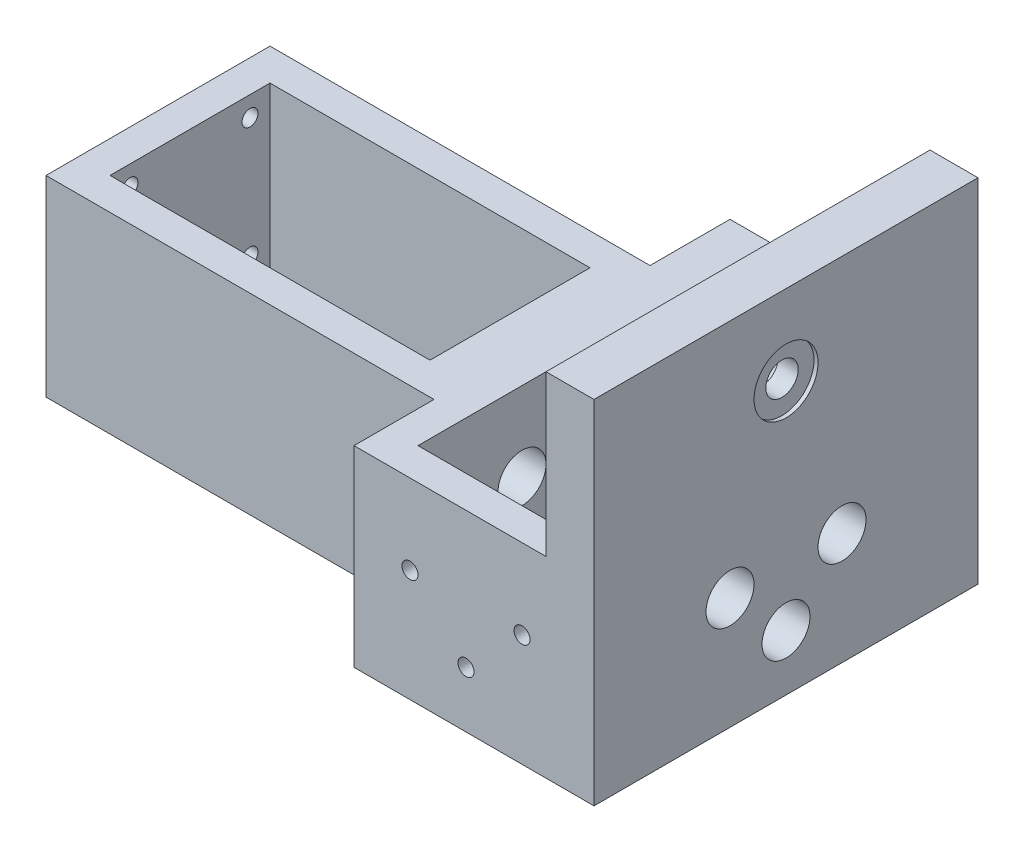
SolidWorks part; units mm, degrees
ref_plane "Front Plane" through (0, 0, 0) normal (0, 0, 1) x (1, 0, 0)
ref_plane "Top Plane" through (0, 0, 0) normal (0, 1, 0) x (1, 0, 0)
ref_plane "Right Plane" through (0, 0, 0) normal (1, 0, 0) x (0, 0, -1)
sketch "Sketch1" plane through (0, 0, 0) normal (0, 1, 0) x (1, 0, 0)
  line L0 (0, 0) -> (0, 20) construction
  line L1 (0, 20) -> (40, 20) construction
  line L2 (40, 20) -> (40, 0) construction
  line L3 (40, 0) -> (0, 0) construction
  line L4 (0, 20) -> (-5, 20) construction
  line L5 (40, 20) -> (45, 20) construction
  line L6 (-5, 20) -> (-5, 0) construction
  line L7 (-5, 0) -> (0, 0) construction
  line L8 (40, 20) -> (48.5, 20) construction
  line L9 (45, 0) -> (40, 0) construction
  line L10 (45, 20) -> (45, 0) construction
  line L11 (40, 0) -> (48.5, 0) construction
  line L12 (48.5, 0) -> (48.5, 20) construction
  line L13 (48.5, 10) -> (48.5, 30) construction
  line L14 (48.5, 10) -> (48.5, -10) construction
  line L15 (48.5, -10) -> (68.5, -10) construction
  line L16 (48.5, 30) -> (68.5, 30) construction
  line L17 (68.5, 30) -> (68.5, -10) construction
  line L18 (48.5, 20) -> (43.5, 20) construction
  line L19 (43.5, 20) -> (43.5, 30) construction
  line L20 (43.5, 30) -> (43.5, 35) construction
  line L21 (43.5, 35) -> (68.5, 35) construction
  line L22 (68.5, 35) -> (73.5, 35) construction
  line L23 (73.5, 35) -> (73.5, -10) construction
  line L24 (73.5, -10) -> (73.5, -15) construction
  line L25 (73.5, -15) -> (43.5, -15) construction
  line L26 (43.5, -15) -> (43.5, 20) construction
  line L27 (-5, 20) -> (43.5, 20)
  line L28 (43.5, 20) -> (43.5, 35)
  line L29 (43.5, 35) -> (73.5, 35)
  line L30 (73.5, 35) -> (73.5, -15)
  line L31 (73.5, -15) -> (43.5, -15)
  line L32 (43.5, -15) -> (43.5, 0)
  line L33 (43.5, 0) -> (-5, 0)
  line L34 (-5, 0) -> (-5, 20)
  line L35 (-5, 10) -> (73.5, 10) construction
extrude "Boss-Extrude1" add sketch "Sketch1" along normal blind 5
sketch "Sketch2" plane through (0, 5, 0) normal (0, 1, 0) x (1, 0, 0)
  line L0 (-5, 20) -> (0, 20) construction
  line L1 (43.5, 20) -> (-5, 20) construction
  line L2 (0, 20) -> (0, 0) construction
  line L3 (0, 0) -> (-5, 0) construction
  line L4 (-5, 0) -> (-5, 20) construction
  line L5 (0, 20) -> (40, 20) construction
  line L6 (40, 20) -> (40, 0) construction
  line L7 (-5, 0) -> (43.5, 0) construction
  line L8 (73.5, 35) -> (68.5, 35) construction
  line L9 (68.5, 35) -> (68.5, -15) construction
  line L10 (43.5, -15) -> (73.5, -15) construction
  line L11 (43.5, 35) -> (48.5, 35) construction
  line L12 (48.5, 35) -> (48.5, -15) construction
  line L13 (43.5, 35) -> (43.5, 30) construction
  line L14 (43.5, 30) -> (73.5, 30) construction
  line L15 (73.5, -15) -> (73.5, 35) construction
  line L16 (73.5, -15) -> (73.5, -10) construction
  line L17 (73.5, -10) -> (43.5, -10) construction
  line L18 (43.5, 0) -> (43.5, -15) construction
  line L19 (40, 20) -> (43.5, 20)
  line L20 (-5, 20) -> (0, 20)
  line L21 (-5, 20) -> (-5, 0)
  line L22 (-5, 0) -> (0, 0)
  line L23 (0, 20) -> (0, 0)
  line L24 (48.5, 30) -> (68.5, 30)
  line L25 (48.5, 30) -> (48.5, -10)
  line L26 (48.5, -10) -> (68.5, -10)
  line L27 (68.5, 30) -> (68.5, -10)
  line L28 (43.5, 20) -> (43.5, 35)
  line L29 (43.5, 35) -> (73.5, 35)
  line L30 (73.5, 35) -> (73.5, -15)
  line L31 (73.5, -15) -> (43.5, -15)
  line L32 (43.5, -15) -> (43.5, 0)
  line L33 (43.5, 0) -> (40, 0)
  line L34 (40, 0) -> (40, 20)
extrude "Boss-Extrude2" add sketch "Sketch2" along normal blind 20
sketch "Sketch3" plane through (0, 0, 0) normal (0, 0, 1) x (1, 0, 0)
  line L0 (43.5, 25) -> (-5, 25)
  line L1 (-5, 25) -> (-5, 0)
  line L2 (-5, 0) -> (43.5, 0)
  line L3 (43.5, 0) -> (43.5, 25)
extrude "Boss-Extrude3" add sketch "Sketch3" along normal blind 4
sketch "Sketch4" plane through (0, 0, -20) normal (0, 0, -1) x (-1, 0, 0)
  line L0 (-43.5, 25) -> (5, 25)
  line L1 (5, 25) -> (5, 0)
  line L2 (5, 0) -> (-43.5, 0)
  line L3 (-43.5, 0) -> (-43.5, 25)
extrude "Boss-Extrude4" add sketch "Sketch4" along normal blind 4
sketch "Sketch6" plane through (0, 0, 0) normal (0, -1, 0) x (1, 0, 0)
  line L0 (73.5, 15) -> (72.5, 15) construction
  line L1 (72.5, 15) -> (72.5, -35) construction
  line L2 (73.5, -35) -> (43.5, -35) construction
  line L3 (73.5, -35) -> (73.5, -34) construction
  line L4 (73.5, -34) -> (43.5, -34) construction
  line L5 (43.5, -35) -> (43.5, -24) construction
  line L6 (43.5, 15) -> (44.5, 15) construction
  line L7 (43.5, 15) -> (73.5, 15) construction
  line L8 (44.5, 15) -> (44.5, 14) construction
  line L9 (72.5, -34) -> (72.5, 14)
  line L10 (72.5, 14) -> (44.5, 14)
  line L11 (43.5, 4) -> (44.5, 4) construction
  line L12 (43.5, 4) -> (44.5, 4)
  line L13 (44.5, 4) -> (44.5, 14)
  line L14 (43.5, 4) -> (42.1751, 8.832)
  line L15 (42.1751, 8.832) -> (-3.5645, 8.832)
  line L16 (-5, 4) -> (-4, 4) construction
  line L17 (-5, 4) -> (43.5, 4) construction
  line L18 (-4, 4) -> (-4, 8.832) construction
  line L19 (-3.5645, 8.832) -> (-4, 4)
  line L20 (-4, 4) -> (-4, -32.6512)
  line L21 (-4, -32.6512) -> (43.5, -34)
  line L22 (43.5, -34) -> (72.5, -34)
  line L24 (-127.2585, 77.6513) -> (166.7327, 77.6513)
  line L25 (-127.2585, 77.6513) -> (-127.2585, -88.9607)
  line L26 (-127.2585, -88.9607) -> (166.7327, -88.9607)
  line L27 (166.7327, 77.6513) -> (166.7327, -88.9607)
extrude "Cut-Extrude1" cut sketch "Sketch6" against normal blind 218
sketch "Sketch7" plane through (0, 25, 0) normal (0, 1, 0) x (1, 0, 0)
  line L0 (44.5, -14) -> (72.5, -14) construction
  line L1 (72.5, 34) -> (68.5, 34)
  line L2 (72.5, 34) -> (72.5, -14)
  line L3 (72.5, -14) -> (68.5, -14)
  line L4 (68.5, 34) -> (68.5, -14)
extrude "Boss-Extrude5" add sketch "Sketch7" along normal blind 20
sketch "Sketch8" plane through (-4, 0, 0) normal (-1, 0, 0) x (0, 0, 1)
  line L0 (-10, 0) -> (-10, 25) construction
  line L1 (4, 0) -> (-24, 0) construction
  line L2 (-24, 25) -> (4, 25) construction
  line L3 (-10, 25) -> (-10, 0) construction
  line L4 (-10, 0) -> (-10, 5) construction
  line L5 (-10, 5) -> (4, 5) construction
  line L6 (4, 25) -> (4, 0) construction
  line L7 (4, 5) -> (4, 25) construction
  line L8 (4, 25) -> (4, 0) construction
  line L9 (-34, 25) -> (-34, 0) construction
  line L10 (14, 0) -> (-34, 0)
  line L11 (14, 0) -> (14, 1)
  line L12 (14, 1) -> (-34, 1)
  line L13 (-34, 0) -> (-34, 1)
extrude "Cut-Extrude2" cut sketch "Sketch8" against normal blind 87
sketch "Sketch9" plane through (-4, 0, 0) normal (-1, 0, 0) x (0, 0, 1)
  line L0 (-10, 25) -> (-10, 1) construction
  line L1 (-24, 25) -> (4, 25) construction
  line L2 (4, 1) -> (-24, 1) construction
  line L3 (-10, 1) -> (-10, 5) construction
  line L4 (-10, 5) -> (4, 5) construction
  line L5 (4, 5) -> (-24, 5) construction
  line L6 (-24, 25) -> (-24, 1) construction
  line L7 (-24, 5) -> (-20, 5) construction
  line L8 (-20, 5) -> (-20, 25) construction
  line L9 (-20, 25) -> (4, 25) construction
  line L10 (4, 25) -> (4, 5) construction
  line L11 (4, 5) -> (0, 5) construction
  line L12 (0, 5) -> (0, 25) construction
  line L13 (-10, 5) -> (-2.5, 5) construction
  line L14 (-2.5, 5) -> (-2.5, 25) construction
  line L15 (-2.5, 25) -> (-17.5, 25) construction
  line L16 (-17.5, 25) -> (-17.5, 5) construction
  line L17 (-2.5, 15) -> (-2.5, 22.5) construction
  line L18 (-2.5, 22.5) -> (-17.5, 22.5) construction
  line L19 (-2.5, 15) -> (-17.5, 15) construction
  circle A0 centre (-2.5, 22.5) radius 1
  circle A1 centre (-17.5, 22.5) radius 1
  circle A2 centre (-17.5, 7.5) radius 1
  circle A3 centre (-2.5, 7.5) radius 1
extrude "Cut-Extrude3" cut sketch "Sketch9" against normal blind 10
sketch "Sketch10" plane through (40, 0, 0) normal (-1, 0, 0) x (0, 0, 1)
  line L0 (-20, 25) -> (0, 25) construction
  line L1 (-20, 25) -> (0, 25) construction
  line L2 (-30, 25) -> (10, 25) construction
  line L3 (0, 25) -> (-10, 25) construction
  line L4 (-10, 25) -> (-10, 1) construction
  line L5 (-34, 1) -> (14, 1) construction
  line L6 (-10, 1) -> (-10, 5) construction
  line L7 (-10, 5) -> (-10, 8) construction
  line L8 (-10, 8) -> (-20, 8) construction
  line L9 (-20, 8) -> (0, 8) construction
  line L10 (0, 25) -> (0, 5) construction
  line L11 (-30, 5) -> (10, 5) construction
  line L12 (0, 5) -> (-20, 5) construction
  line L13 (-20, 5) -> (-20, 25) construction
  line L14 (-20, 25) -> (-17, 25) construction
  line L15 (-17, 25) -> (-17, 5) construction
  line L16 (-3, 25) -> (-3, 5) construction
  line L17 (0, 5) -> (0, 25) construction
  line L18 (-10, 8) -> (-17, 15) construction
  line L19 (-10, 8) -> (-3, 15) construction
  circle A0 centre (-3, 15) radius 1
  circle A1 centre (-10, 8) radius 1
  circle A2 centre (-17, 15) radius 1
extrude "Cut-Extrude4" cut sketch "Sketch10" against normal blind 60
sketch "Sketch12" plane through (72.5, 0, 0) normal (1, 0, 0) x (0, 0, -1)
  line L0 (5.1213, 17.1213) -> (12.1213, 10.1213) construction
  line L1 (0.8787, 12.8787) -> (7.8787, 5.8787) construction
  line L2 (3, 18) -> (17, 18) construction
  line L3 (17, 12) -> (3, 12) construction
  circle A0 centre (17, 15) radius 3
  circle A1 centre (10, 8) radius 3
  circle A2 centre (3, 15) radius 3
extrude "Cut-Extrude5" cut sketch "Sketch12" against normal blind 29.5
sketch "Sketch13" plane through (0, 0, 14) normal (0, 0, 1) x (1, 0, 0)
  line L0 (72.5, 1) -> (68.5, 1) construction
  line L1 (44.5, 1) -> (-4, 1) construction
  line L2 (68.5, 1) -> (68.5, 25) construction
  line L3 (68.5, 25) -> (68.5, 1) construction
  line L4 (68.5, 1) -> (68.5, 5) construction
  line L5 (68.5, 5) -> (44.5, 5) construction
  line L6 (44.5, 25) -> (44.5, 1) construction
  line L7 (44.5, 5) -> (48.5, 5) construction
  line L8 (48.5, 5) -> (48.5, 25) construction
  line L9 (68.5, 25) -> (48.5, 25) construction
  line L10 (48.5, 25) -> (58.5, 25) construction
  line L11 (58.5, 25) -> (58.5, 8) construction
  line L12 (58.5, 8) -> (65.5, 15) construction
  line L13 (58.5, 8) -> (51.5, 15) construction
  line L14 (65.5, 15) -> (51.5, 15) construction
  line L15 (68.5, 5) -> (65.5, 5) construction
  line L16 (65.5, 5) -> (65.5, 15) construction
  circle A0 centre (58.5, 8) radius 1
  circle A1 centre (51.5, 15) radius 1
  circle A2 centre (65.5, 15) radius 1
extrude "Cut-Extrude6" cut sketch "Sketch13" against normal blind 29.5
sketch "Sketch14" plane through (0, 0, -30) normal (0, 0, 1) x (1, 0, 0)
  line L0 (48.5, 25) -> (68.5, 25) construction
  line L1 (68.5, 25) -> (43.5, 25) construction
  line L2 (68.5, 25) -> (48.5, 25) construction
  line L3 (68.5, 25) -> (68.5, 5) construction
  line L4 (68.5, 5) -> (48.5, 5) construction
  line L5 (48.5, 5) -> (48.5, 25) construction
  line L6 (48.5, 25) -> (68.5, 5) construction
  line L7 (68.5, 5) -> (68.5, 25) construction
  line L8 (68.5, 25) -> (48.5, 5) construction
  line L9 (58.5, 15) -> (58.5, 22.5) construction
  line L10 (58.5, 22.5) -> (68.5, 22.5) construction
  line L11 (68.5, 22.5) -> (48.5, 22.5) construction
  line L12 (66, 22.5) -> (66, 7.5) construction
  line L13 (66, 7.5) -> (51, 7.5) construction
  line L14 (51, 7.5) -> (51, 22.5) construction
  circle A0 centre (66, 22.5) radius 1
  circle A1 centre (66, 7.5) radius 1
  circle A2 centre (51, 7.5) radius 1
  circle A3 centre (51, 22.5) radius 1
extrude "Cut-Extrude7" cut sketch "Sketch14" against normal blind 29.5
sketch "Sketch15" plane through (72.5, 0, 0) normal (1, 0, 0) x (0, 0, -1)
  line L0 (10, 1) -> (10, 45) construction
  line L1 (34, 1) -> (-14, 1) construction
  line L2 (-14, 45) -> (34, 45) construction
  line L3 (10, 45) -> (10, 35) construction
  circle A0 centre (10, 35) radius 1.775
extrude "Cut-Extrude8" cut sketch "Sketch15" against normal blind 29.5
sketch "Sketch16" plane through (68.5, 0, 0) normal (-1, 0, 0) x (0, 0, 1)
  circle A0 centre (-10, 35) radius 2.025
extrude "Cut-Extrude9" cut sketch "Sketch16" against normal blind 29.5
sketch "Sketch17" plane through (68.5, 0, 0) normal (-1, 0, 0) x (0, 0, 1)
  circle A0 centre (-10, 35) radius 3.5
extrude "Cut-Extrude10" cut sketch "Sketch17" against normal blind 3
sketch "Sketch18" plane through (72.5, 0, 0) normal (1, 0, 0) x (0, 0, -1)
  line L4 (-14, 1) -> (34, 1)
  line L5 (34, 1) -> (34, 45)
  line L6 (34, 45) -> (-14, 45)
  line L7 (-14, 45) -> (-14, 1)
  line L8 (-14, 1) -> (34, 1)
  line L9 (34, 1) -> (34, 45)
  line L10 (34, 45) -> (-14, 45)
  line L11 (-14, 45) -> (-14, 1)
  circle A0 centre (10, 35) radius 2.025 construction
  circle A1 centre (10, 35) radius 2.025
  circle A2 centre (17, 15) radius 3 construction
  circle A3 centre (17, 15) radius 3
  circle A4 centre (10, 8) radius 3 construction
  circle A5 centre (10, 8) radius 3
  circle A6 centre (3, 15) radius 3 construction
  circle A7 centre (3, 15) radius 3
  dimension "D1" = 0
extrude "Boss-Extrude6" add sketch "Sketch18" along normal blind 2
ref_plane "Plano1" through (-4, 25, -24) normal (1, 0, 0) x (0, 0, -1)
sketch "Croquis1" plane through (-4, 25, -24) normal (1, 0, 0) x (0, 0, -1)
  circle A0 centre (-14, 10) radius 4
sketch "Croquis2" plane through (74.5, 0, 0) normal (1, 0, 0) x (0, 0, -1)
  circle A0 centre (10, 35) radius 4
extrude "Cortar-Extruir2" cut sketch "Croquis2" against normal blind 0.5
